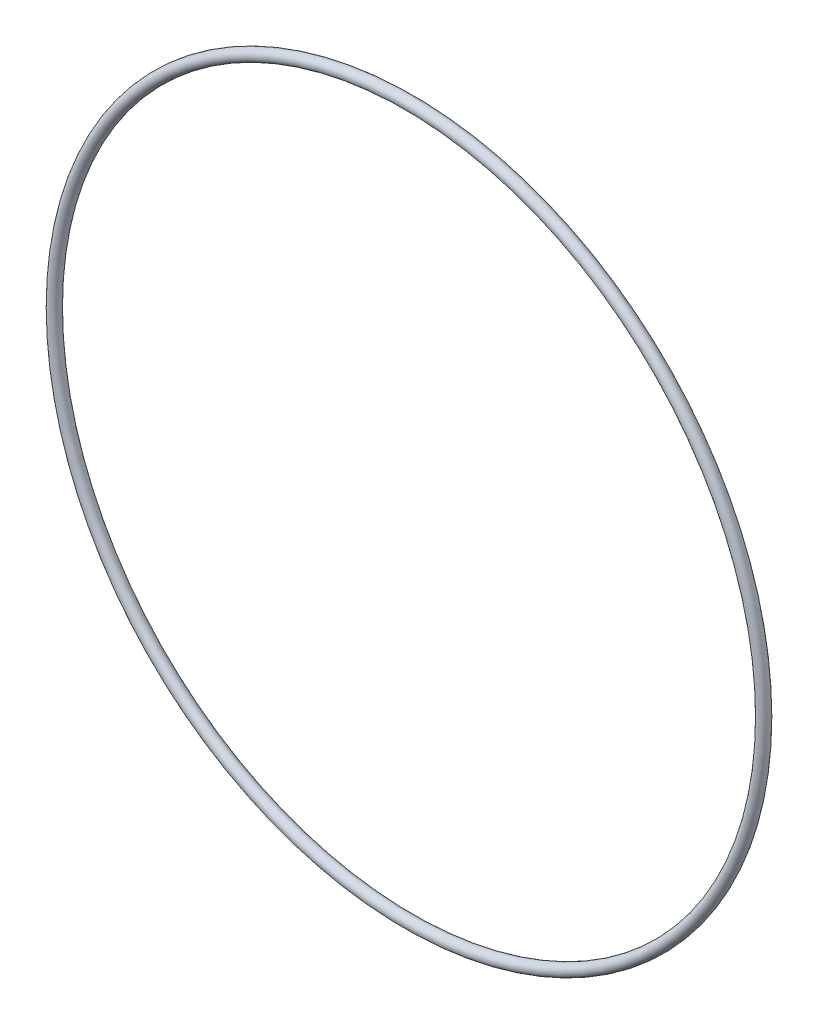
SolidWorks part; units mm, degrees
material "Rubber"
ref_plane "Front" through (0, 0, 0) normal (0, 0, 1) x (1, 0, 0)
ref_plane "Top" through (0, 0, 0) normal (0, 1, 0) x (1, 0, 0)
ref_plane "Right" through (0, 0, 0) normal (1, 0, 0) x (0, 0, -1)
sketch "Sketch1" plane through (0, 0, 0) normal (1, 0, 0) x (0, -1, 0)
  line L0 (0, -0.889) -> (0, 0.889) construction
  line L2 (-61.1746, 0) -> (61.1746, 0) construction
  line L3 (-53.8353, 0) -> (53.8353, 0) construction
  circle A0 centre (54.7243, 0) radius 0.889
  point P9 (53.8353, 0)
  point P10 (55.6133, 0)
  point P13 (54.7243, 0.889)
  point P14 (54.7243, -0.889)
  dimension "Width" = 1.778
  dimension "ID" = 107.6706
revolve "Revolve1" add sketch "Sketch1" angle 360 about L0
